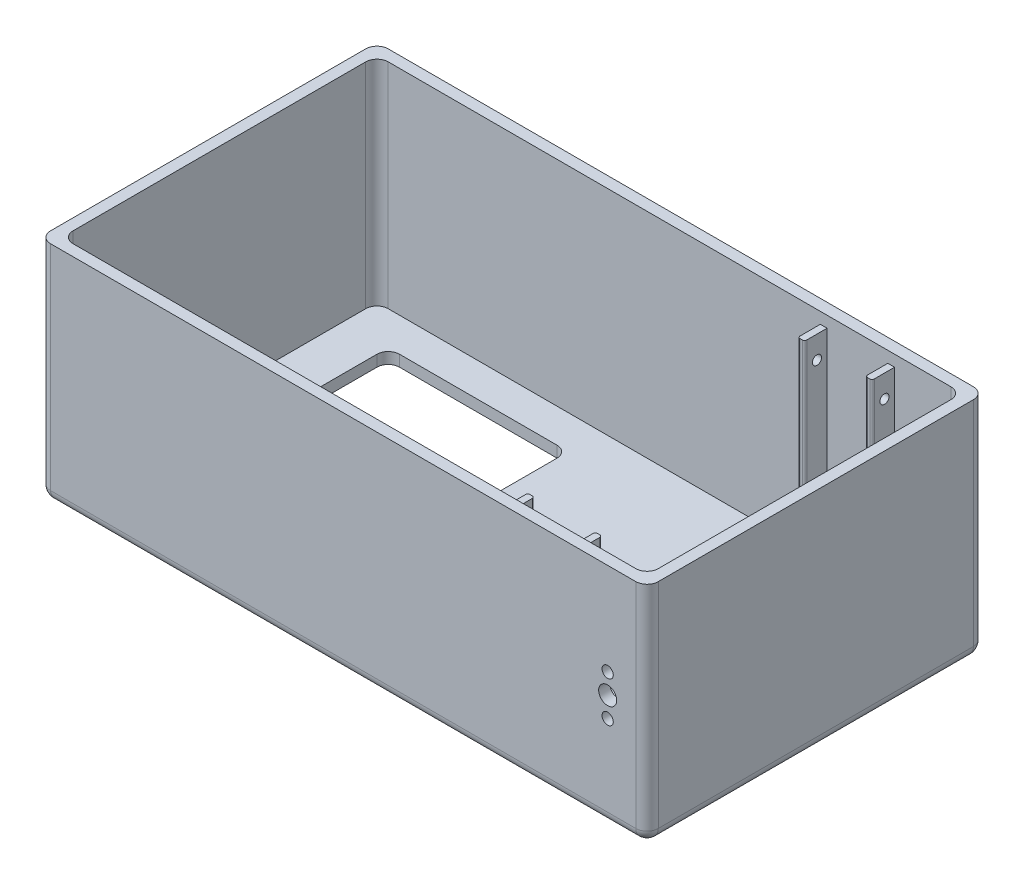
SolidWorks part; units mm, degrees
ref_plane "Front Plane" through (0, 0, 0) normal (0, 0, 1) x (1, 0, 0)
ref_plane "Top Plane" through (0, 0, 0) normal (0, 1, 0) x (1, 0, 0)
ref_plane "Right Plane" through (0, 0, 0) normal (1, 0, 0) x (0, 0, -1)
sketch "Sketch1" plane through (0, 0, 0) normal (0, 1, 0) x (1, 0, 0)
  line L1 (-135, -75) -> (135, -75)
  line L2 (-135, -75) -> (-135, 75)
  line L3 (-135, 75) -> (135, 75)
  line L4 (135, -75) -> (135, 75)
  line L5 (-135, -75) -> (135, 75) construction
  line L6 (-135, 75) -> (135, -75) construction
  point P0 (0, 0)
  dimension "D1" = 150
  dimension "D2" = 270
extrude "Outer Box" add sketch "Sketch1" along normal blind 100
sketch "Sketch2" plane through (0, 100, 0) normal (0, 1, 0) x (1, 0, 0)
  line L8 (130, -70) -> (130, 70)
  line L9 (130, 70) -> (-130, 70)
  line L10 (-130, 70) -> (-130, -70)
  line L11 (-130, -70) -> (130, -70)
  line L12 (130, -70) -> (130, 70)
  line L13 (130, 70) -> (-130, 70)
  line L14 (-130, 70) -> (-130, -70)
  line L15 (-130, -70) -> (130, -70)
  dimension "D1" = 5
extrude "Inner Box" cut sketch "Sketch2" against normal blind 95
fillet "Fillet2" radius 5 12 edges at (-135, 0, 0) (135, 0, 0) (0, 0, -75) (-135, 50, -75) (135, 50, -75) (135, 50, 75) (0, 0, 75) (-135, 50, 75) (130, 52.5, -70) (130, 52.5, 70) (-130, 52.5, 70) (-130, 52.5, -70)
sketch "Sketch3" plane through (0, 0, 0) normal (0, -1, 0) x (1, 0, 0)
  line L1 (-110, 55) -> (-30, 55)
  line L2 (-110, 55) -> (-110, -55)
  line L3 (-110, -55) -> (-30, -55)
  line L4 (-30, 55) -> (-30, -55)
  line L5 (130, -75) -> (-130, -75) construction
  line L6 (-135, -70) -> (-135, 70) construction
  dimension "D1" = 110
  dimension "D2" = 80
  dimension "D3" = 20
  dimension "D4" = 25
extrude "Screen Hole" cut sketch "Sketch3" against normal blind 77
fillet "Fillet3" radius 5 4 edges at (-110, 2.5, 55) (-110, 2.5, -55) (-30, 2.5, -55) (-30, 2.5, 55)
sketch "Sketch4" plane through (0, 0, 75) normal (0, 0, 1) x (1, 0, 0)
  line L0 (130, 5) -> (130, 100) construction
  line L2 (130, 0) -> (-130, 0) construction
  circle A0 centre (117.5, 50) radius 4
  circle A1 centre (117.5, 41) radius 2.5
  circle A2 centre (117.5, 59) radius 2.5
  point P4 (130, 52.5)
  point P9 (0, 0)
  point P10 (0, 0)
  point P13 (0, 0)
  dimension "D1" = 12.5
  dimension "D3" = 9
  dimension "D4" = 2
  dimension "D2" = 50
extrude "Wheel Holes" cut sketch "Sketch4" against normal through all
sketch "Sketch5" plane through (0, 0, 0) normal (0, -1, 0) x (1, 0, 0)
  circle A0 centre (0, 0) radius 14.5
extrude "Cut-Extrude4" cut sketch "Sketch5" against normal through all
sketch "Sketch8" plane through (0, 0, 0) normal (0, -1, 0) x (1, 0, 0)
  line L1 (22.7185, 62.7804) -> (55.7185, 62.7804) construction
  line L2 (22.7185, 62.7804) -> (22.7185, 12.7804) construction
  line L3 (22.7185, 12.7804) -> (55.7185, 12.7804) construction
  line L4 (55.7185, 62.7804) -> (55.7185, 12.7804) construction
  dimension "D1" = 50
  dimension "D2" = 33
sketch "Sketch9" plane through (0, 0, 0) normal (0, -1, 0) x (1, 0, 0)
  line L0 (22.7185, 62.7804) -> (55.7185, 62.7804) construction
  line L1 (22.7185, 62.7804) -> (22.7185, 12.7804) construction
  circle A0 centre (22.7185, 62.7804) radius 1
  circle A1 centre (26.7185, 62.7804) radius 1
  circle A2 centre (30.7185, 62.7804) radius 1
  circle A3 centre (34.7185, 62.7804) radius 1
  circle A4 centre (38.7185, 62.7804) radius 1
  circle A5 centre (42.7185, 62.7804) radius 1
  circle A6 centre (46.7185, 62.7804) radius 1
  circle A7 centre (50.7185, 62.7804) radius 1
  circle A8 centre (54.7185, 62.7804) radius 1
  circle A9 centre (58.7185, 62.7804) radius 1
  circle A10 centre (26.7185, 57.7804) radius 1
  circle A11 centre (30.7185, 57.7804) radius 1
  circle A12 centre (34.7185, 57.7804) radius 1
  circle A13 centre (38.7185, 57.7804) radius 1
  circle A14 centre (42.7185, 57.7804) radius 1
  circle A15 centre (46.7185, 57.7804) radius 1
  circle A16 centre (50.7185, 57.7804) radius 1
  circle A17 centre (54.7185, 57.7804) radius 1
  circle A18 centre (58.7185, 57.7804) radius 1
  circle A19 centre (26.7185, 52.7804) radius 1
  circle A20 centre (30.7185, 52.7804) radius 1
  circle A21 centre (34.7185, 52.7804) radius 1
  circle A22 centre (38.7185, 52.7804) radius 1
  circle A23 centre (42.7185, 52.7804) radius 1
  circle A24 centre (46.7185, 52.7804) radius 1
  circle A25 centre (50.7185, 52.7804) radius 1
  circle A26 centre (54.7185, 52.7804) radius 1
  circle A27 centre (58.7185, 52.7804) radius 1
  circle A28 centre (26.7185, 47.7804) radius 1
  circle A29 centre (30.7185, 47.7804) radius 1
  circle A30 centre (34.7185, 47.7804) radius 1
  circle A31 centre (38.7185, 47.7804) radius 1
  circle A32 centre (42.7185, 47.7804) radius 1
  circle A33 centre (46.7185, 47.7804) radius 1
  circle A34 centre (50.7185, 47.7804) radius 1
  circle A35 centre (54.7185, 47.7804) radius 1
  circle A36 centre (58.7185, 47.7804) radius 1
  circle A37 centre (26.7185, 42.7804) radius 1
  circle A38 centre (30.7185, 42.7804) radius 1
  circle A39 centre (34.7185, 42.7804) radius 1
  circle A40 centre (38.7185, 42.7804) radius 1
  circle A41 centre (42.7185, 42.7804) radius 1
  circle A42 centre (46.7185, 42.7804) radius 1
  circle A43 centre (50.7185, 42.7804) radius 1
  circle A44 centre (54.7185, 42.7804) radius 1
  circle A45 centre (58.7185, 42.7804) radius 1
  circle A46 centre (26.7185, 37.7804) radius 1
  circle A47 centre (30.7185, 37.7804) radius 1
  circle A48 centre (34.7185, 37.7804) radius 1
  circle A49 centre (38.7185, 37.7804) radius 1
  circle A50 centre (42.7185, 37.7804) radius 1
  circle A51 centre (46.7185, 37.7804) radius 1
  circle A52 centre (50.7185, 37.7804) radius 1
  circle A53 centre (54.7185, 37.7804) radius 1
  circle A54 centre (58.7185, 37.7804) radius 1
  circle A55 centre (26.7185, 32.7804) radius 1
  circle A56 centre (30.7185, 32.7804) radius 1
  circle A57 centre (34.7185, 32.7804) radius 1
  circle A58 centre (38.7185, 32.7804) radius 1
  circle A59 centre (42.7185, 32.7804) radius 1
  circle A60 centre (46.7185, 32.7804) radius 1
  circle A61 centre (50.7185, 32.7804) radius 1
  circle A62 centre (54.7185, 32.7804) radius 1
  circle A63 centre (58.7185, 32.7804) radius 1
  circle A64 centre (26.7185, 27.7804) radius 1
  circle A65 centre (30.7185, 27.7804) radius 1
  circle A66 centre (34.7185, 27.7804) radius 1
  circle A67 centre (38.7185, 27.7804) radius 1
  circle A68 centre (42.7185, 27.7804) radius 1
  circle A69 centre (46.7185, 27.7804) radius 1
  circle A70 centre (50.7185, 27.7804) radius 1
  circle A71 centre (54.7185, 27.7804) radius 1
  circle A72 centre (58.7185, 27.7804) radius 1
  circle A73 centre (26.7185, 22.7804) radius 1
  circle A74 centre (30.7185, 22.7804) radius 1
  circle A75 centre (34.7185, 22.7804) radius 1
  circle A76 centre (38.7185, 22.7804) radius 1
  circle A77 centre (42.7185, 22.7804) radius 1
  circle A78 centre (46.7185, 22.7804) radius 1
  circle A79 centre (50.7185, 22.7804) radius 1
  circle A80 centre (54.7185, 22.7804) radius 1
  circle A81 centre (58.7185, 22.7804) radius 1
  circle A82 centre (26.7185, 17.7804) radius 1
  circle A83 centre (30.7185, 17.7804) radius 1
  circle A84 centre (34.7185, 17.7804) radius 1
  circle A85 centre (38.7185, 17.7804) radius 1
  circle A86 centre (42.7185, 17.7804) radius 1
  circle A87 centre (46.7185, 17.7804) radius 1
  circle A88 centre (50.7185, 17.7804) radius 1
  circle A89 centre (54.7185, 17.7804) radius 1
  circle A90 centre (58.7185, 17.7804) radius 1
  circle A91 centre (26.7185, 12.7804) radius 1
  circle A92 centre (30.7185, 12.7804) radius 1
  circle A93 centre (34.7185, 12.7804) radius 1
  circle A94 centre (38.7185, 12.7804) radius 1
  circle A95 centre (42.7185, 12.7804) radius 1
  circle A96 centre (46.7185, 12.7804) radius 1
  circle A97 centre (50.7185, 12.7804) radius 1
  circle A98 centre (54.7185, 12.7804) radius 1
  circle A99 centre (58.7185, 12.7804) radius 1
  circle A100 centre (22.7185, 57.7804) radius 1
  circle A101 centre (22.7185, 52.7804) radius 1
  circle A102 centre (22.7185, 47.7804) radius 1
  circle A103 centre (22.7185, 42.7804) radius 1
  circle A104 centre (22.7185, 37.7804) radius 1
  circle A105 centre (22.7185, 32.7804) radius 1
  circle A106 centre (22.7185, 27.7804) radius 1
  circle A107 centre (22.7185, 22.7804) radius 1
  circle A108 centre (22.7185, 17.7804) radius 1
  circle A109 centre (22.7185, 12.7804) radius 1
  dimension "D1" = 0
  dimension "D2" = 0
  dimension "D3" = 10
  dimension "D4" = 11
extrude "Cut-Extrude5" cut sketch "Sketch9" against normal through all
sketch "Sketch10" plane through (0, 0, -70) normal (0, 0, 1) x (1, 0, 0)
  line L0 (130, 100) -> (130, 5) construction
  line L1 (97, 95) -> (100, 95)
  line L2 (97, 95) -> (97, 5)
  line L3 (97, 5) -> (100, 5)
  line L4 (100, 95) -> (100, 5)
  line L5 (125, 5) -> (-125, 5) construction
  dimension "D1" = 30
  dimension "D2" = 3
  dimension "D3" = 90
extrude "Boss-Extrude2" add sketch "Sketch10" along normal blind 10
sketch "Sketch11" plane through (0, 0, 70) normal (0, 0, -1) x (-1, 0, 0)
  line L0 (-130, 5) -> (-130, 100) construction
  line L1 (-97, 95) -> (-100, 95)
  line L2 (-97, 95) -> (-97, 5)
  line L3 (-97, 5) -> (-100, 5)
  line L4 (-100, 95) -> (-100, 5)
  line L5 (125, 5) -> (-125, 5) construction
  dimension "D1" = 30
  dimension "D2" = 3
  dimension "D3" = 90
extrude "Boss-Extrude3" add sketch "Sketch11" along normal blind 10
pattern_linear "LPattern1" count 2 spacing 30 along (-1, 0, 0) of "Boss-Extrude2", "Boss-Extrude3"
fillet "Fillet4" radius 1 8 edges at (100, 50, -60) (97, 50, -60) (100, 50, 60) (97, 50, 60) (70, 50, -60) (67, 50, -60) (70, 50, 60) (67, 50, 60)
sketch "Sketch13" plane through (97, 0, 0) normal (-1, 0, 0) x (0, 0, 1)
  line L0 (-61, 85) -> (-70, 85) construction
  line L1 (-61, 5) -> (-61, 95) construction
  line L2 (-70, 95) -> (-70, 5) construction
  line L3 (-61, 95) -> (-70, 95) construction
  line L5 (-61, 15) -> (-70, 15) construction
  line L6 (-61, 5) -> (-70, 5) construction
  circle A0 centre (-65.5, 85) radius 2.0249
  circle A1 centre (-65.5, 15) radius 2
  point P14 (0, 0)
  dimension "D1" = 10
  dimension "D2" = 10
extrude "Cut-Extrude6" cut sketch "Sketch13" against normal blind 11 and the other way blind 60
sketch "Sketch14" plane through (97, 0, 0) normal (-1, 0, 0) x (0, 0, 1)
  line L0 (61, 85) -> (70, 85) construction
  line L1 (61, 95) -> (61, 5) construction
  line L2 (70, 5) -> (70, 95) construction
  line L3 (61, 15) -> (70, 15) construction
  line L4 (61, 95) -> (70, 95) construction
  line L5 (61, 5) -> (70, 5) construction
  circle A0 centre (65.5, 85) radius 2
  circle A1 centre (65.5, 15) radius 2
  point P12 (0, 0)
  point P13 (0, 0)
  dimension "D1" = 10
  dimension "D2" = 10
extrude "Cut-Extrude7" cut sketch "Sketch14" against normal blind 16 and the other way blind 63
